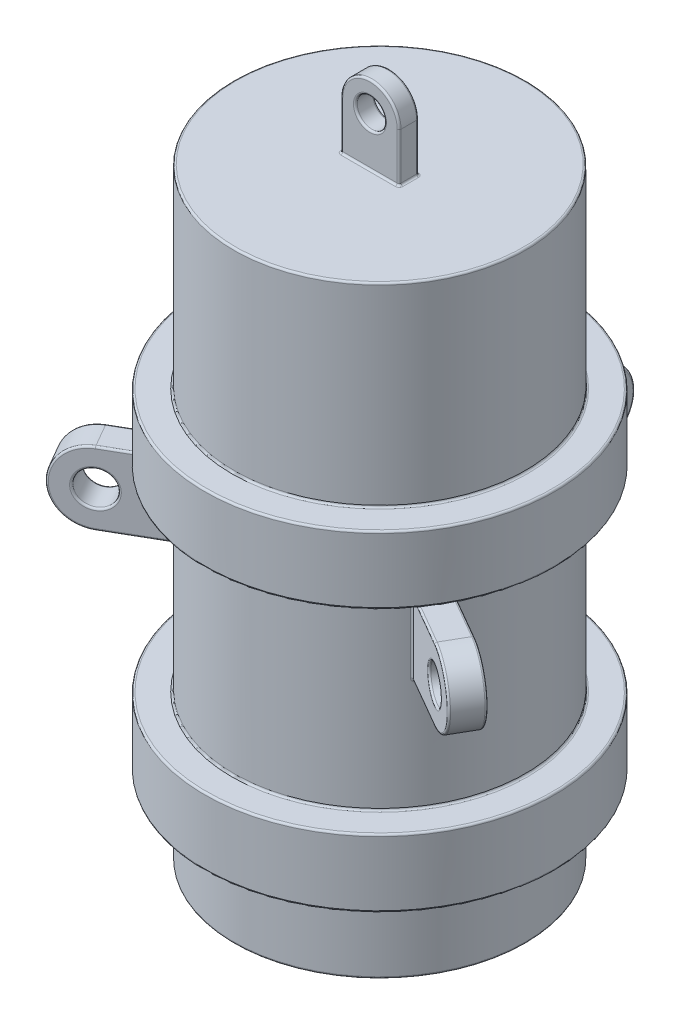
SolidWorks part; units mm, degrees
ref_plane "Front Plane" through (0, 0, 0) normal (0, 0, 1) x (1, 0, 0)
ref_plane "Top Plane" through (0, 0, 0) normal (0, 1, 0) x (1, 0, 0)
ref_plane "Right Plane" through (0, 0, 0) normal (1, 0, 0) x (0, 0, -1)
sketch "Sketch1" plane through (0, 0, 0) normal (0, 0, 1) x (1, 0, 0)
  line L0 (0, 32.9143) -> (0, -29.0857) construction
  line L1 (-4, -29.0857) -> (-15, -29.0857)
  line L2 (-15, -29.0857) -> (-15, -21.0857)
  line L3 (-15, -21.0857) -> (-18, -21.0857)
  line L4 (-18, -21.0857) -> (-18, -14.0857)
  line L5 (-18, -14.0857) -> (-15, -14.0857)
  line L6 (-15, -14.0857) -> (-15, 5.9143)
  line L7 (-15, 5.9143) -> (-18, 5.9143)
  line L8 (-18, 5.9143) -> (-18, 12.9143)
  line L9 (-18, 12.9143) -> (-15, 12.9143)
  line L10 (-15, 12.9143) -> (-15, 32.9143)
  line L11 (-15, 32.9143) -> (0, 32.9143)
  line L12 (-4, -28.0857) -> (-14, -28.0857)
  line L13 (-14, -28.0857) -> (-14, -20.0857)
  line L14 (-14, -20.0857) -> (-17, -20.0857)
  line L15 (-17, -20.0857) -> (-17, -15.0857)
  line L16 (-17, -15.0857) -> (-14, -15.0857)
  line L17 (-14, -15.0857) -> (-14, 6.9143)
  line L18 (-14, 6.9143) -> (-17, 6.9143)
  line L19 (-17, 6.9143) -> (-17, 11.9143)
  line L20 (-17, 11.9143) -> (-14, 11.9143)
  line L21 (-14, 11.9143) -> (-14, 31.9143)
  line L22 (-14, 31.9143) -> (0, 31.9143)
  line L23 (-4, -28.0857) -> (-4, -29.0857)
  line L24 (0, 32.9143) -> (0, 31.9143)
  point P16 (-15, -4.0857)
  dimension "D1" = 4
  dimension "D2" = 11
  dimension "D3" = 8
  dimension "D4" = 20
  dimension "D5" = 7
  dimension "D6" = 20
  dimension "D7" = 7
  dimension "D8" = 3
  dimension "D9" = 1
revolve "Revolve1" add sketch "Sketch1" angle 360 about L24
sketch "Sketch2" plane through (0, 0, 0) normal (0, 0, 1) x (1, 0, 0)
  line L0 (15, 32.9143) -> (-15, 32.9143) construction
  line L1 (3, 37.9143) -> (3, 32.9143)
  line L2 (3, 32.9143) -> (-3, 32.9143)
  line L3 (-3, 32.9143) -> (-3, 37.9143)
  circle A0 centre (0, 37.9143) radius 1.5
  arc A1 (-3, 37.9143) -> (3, 37.9143) centre (0, 37.9143) cw
  dimension "D1" = 3
  dimension "D3" = 0
  dimension "D4" = 1.5
  dimension "D2" = 5
extrude "Boss-Extrude1" add sketch "Sketch2" along normal mid plane 2
sketch "Sketch3" plane through (0, 0, 0) normal (1, 0, 0) x (0, 0, -1)
  line L0 (14, 4.9143) -> (21, 4.9143)
  line L1 (14, -15.0857) -> (14, 6.9143) construction
  line L3 (21, -2.5857) -> (14, -2.5857)
  line L4 (14, -15.0857) -> (14, 6.9143) construction
  line L5 (14, -2.5857) -> (14, 4.9143)
  line L6 (-18, 5.9143) -> (18, 5.9143) construction
  circle A0 centre (21, 1.1643) radius 1.75
  arc A1 (21, 4.9143) -> (21, -2.5857) centre (21, 1.1643) cw
  dimension "D4" = 2
  dimension "D1" = 7
  dimension "D2" = 7.5
  dimension "D3" = 1
extrude "Boss-Extrude2" add sketch "Sketch3" along normal mid plane 3
pattern_circular "CirPattern1" count 3 over 360 about axis through (0, 0, 0) along (0, 1, 0) of "Boss-Extrude2"
fillet "Fillet2" radius 0.2 70 edges at (20.4521, 1.1643, 10.076) (18.9521, 1.1643, 12.674) (16.3059, -2.5857, 7.6822) (22.1841, 1.1643, 11.076) (16.3059, 4.9143, 7.6822) (14.8059, -2.5857, 10.2802) (20.6841, 1.1643, 13.674) (14.8059, 4.9143, 10.2802) (12.9904, 4.9143, 7.5) (12.9904, -2.5857, 7.5) (-18.9521, 1.1643, 12.674) (-20.4521, 1.1643, 10.076) (-14.8059, -2.5857, 10.2802) (-20.6841, 1.1643, 13.674) (-14.8059, 4.9143, 10.2802) (-16.3059, -2.5857, 7.6822) (-22.1841, 1.1643, 11.076) (-16.3059, 4.9143, 7.6822) (-12.9904, 4.9143, 7.5) (-12.9904, -2.5857, 7.5) (-1.5, 1.1643, -22.75) (1.5, 1.1643, -22.75) (-1.5, -2.5857, -17.9624) (-1.5, 1.1643, -24.75) (-1.5, 4.9143, -17.9624) (1.5, -2.5857, -17.9624) (1.5, 1.1643, -24.75) (1.5, 4.9143, -17.9624) (0, 4.9143, -15) (0, -2.5857, -15) (1.5, 37.9143, -1) (1.5, 37.9143, 1) (0, 40.9143, -1) (-3, 35.4143, -1) (0, 32.9143, -1) (3, 35.4143, -1) (0, 40.9143, 1) (-3, 35.4143, 1) (0, 32.9143, 1) (3, 35.4143, 1) (3, 32.9143, 0) (-3, 32.9143, 0) (-14, 31.9143, 0) (-14, 11.9143, 0) (-17, 11.9143, 0) (-17, 6.9143, 0) (-14, 6.9143, 0) (-14, -15.0857, 0) (-17, -15.0857, 0) (-17, -20.0857, 0) (-14, -20.0857, 0) (-14, -28.0857, 0) (-4, -28.0857, 0) (-4, -29.0857, 0) (-15, -29.0857, 0) (-15, -21.0857, 0) (-18, -21.0857, 0) (-18, -14.0857, 0) (-15, -14.0857, 0) (-15, 5.9143, 0) (-18, 5.9143, 0) (-18, 12.9143, 0) (-15, 12.9143, 0) (-1.5, 1.1643, -14.9248) (1.5, 1.1643, -14.9248) (-12.1753, 1.1643, 8.7614) (-13.6753, 1.1643, 6.1634) (13.6753, 1.1643, 6.1634) (12.1753, 1.1643, 8.7614) (-15, 32.9143, 0)
